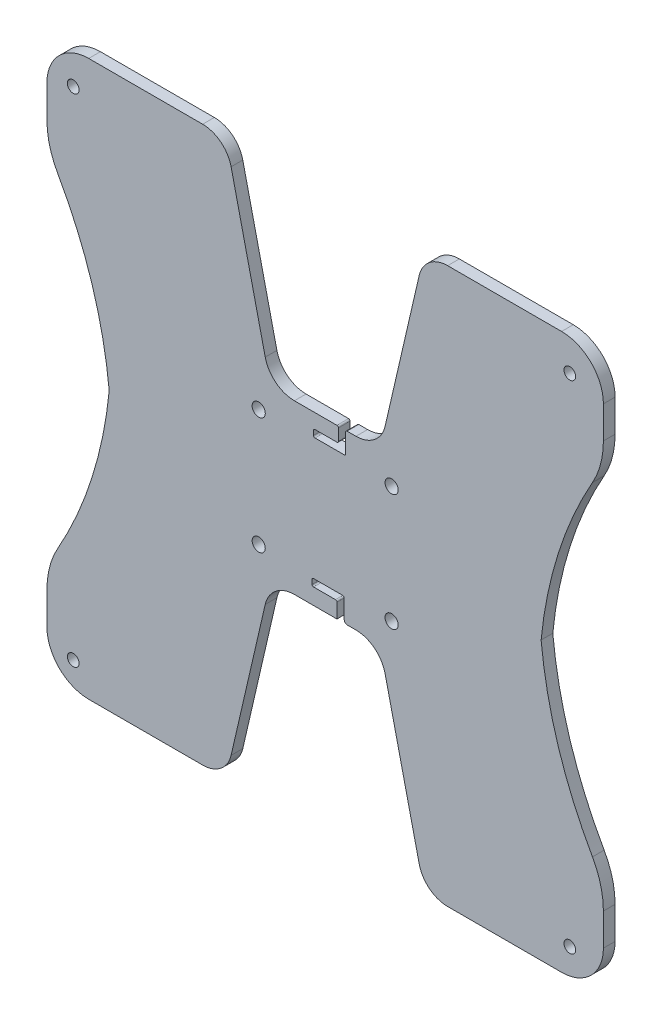
SolidWorks part; units mm, degrees
ref_plane "Front Plane" through (0, 0, 0) normal (0, 0, 1) x (1, 0, 0)
ref_plane "Top Plane" through (0, 0, 0) normal (0, 1, 0) x (1, 0, 0)
ref_plane "Right Plane" through (0, 0, 0) normal (1, 0, 0) x (0, 0, -1)
sketch "Sketch2" plane through (0, 0, 0) normal (0, 0, 1) x (1, 0, 0)
  line L3 (94.3754, -52.7044) -> (94.3754, -56.7044)
  line L4 (93.8754, -57.2044) -> (86.3754, -57.2044)
  line L5 (85.8754, -57.7044) -> (85.8754, -59.2044)
  line L6 (86.3754, -59.7044) -> (96.3754, -59.7044)
  line L7 (96.8754, -59.2044) -> (96.8754, -52.7044)
  line L8 (97.3754, -52.2044) -> (100.3754, -52.2044)
  line L9 (110.3627, -44.2602) -> (122.0425, 6.3307)
  line L10 (131.7862, 14.0812) -> (170.7845, 14.0812)
  line L11 (185.0955, -0.2297) -> (185.0955, -11.2297)
  line L16 (96.3754, -108.6331) -> (96.3754, -102.1331)
  line L17 (95.8754, -101.6331) -> (85.8754, -101.6331)
  line L18 (85.3754, -102.1331) -> (85.3754, -103.6331)
  line L19 (85.8754, -104.1331) -> (93.3754, -104.1331)
  line L20 (93.8754, -104.6331) -> (93.8754, -108.6331)
  line L26 (163.7717, -80.9188) -> (-81.9172, -80.9188) construction
  line L27 (97.3754, -109.6331) -> (100.3754, -109.6331)
  line L28 (185.0955, -161.6078) -> (185.0955, -150.6078)
  line L29 (131.7862, -175.9188) -> (170.7845, -175.9188)
  line L30 (110.3627, -117.5774) -> (122.0425, -168.1683)
  line L31 (185.0955, -161.6078) -> (-5.4045, -161.6078) construction
  line L32 (89.8455, -161.6078) -> (89.8455, -80.9188) construction
  line L33 (82.3155, -52.2044) -> (79.3155, -52.2044)
  line L34 (82.3155, -109.6331) -> (79.3155, -109.6331)
  line L35 (15.9192, -80.9188) -> (261.6081, -80.9188) construction
  line L36 (69.3282, -117.5774) -> (57.6484, -168.1683)
  line L37 (47.9047, -175.9188) -> (8.9064, -175.9188)
  line L38 (-5.4045, -161.6078) -> (-5.4045, -150.6078)
  line L39 (-5.4045, -0.2297) -> (-5.4045, -11.2297)
  line L40 (47.9047, 14.0812) -> (8.9064, 14.0812)
  line L41 (69.3282, -44.2602) -> (57.6484, 6.3307)
  line L42 (82.3155, -52.2044) -> (93.8754, -52.2044)
  line L43 (82.3155, -109.6331) -> (93.8754, -109.6331)
  line L44 (93.8754, -108.6331) -> (93.8754, -109.6331)
  line L45 (142.4554, -175.9188) -> (142.4554, 14.0812) construction
  arc A2 (94.3754, -52.7044) -> (93.8754, -52.2044) centre (93.8754, -52.7044) ccw
  arc A3 (93.8754, -57.2044) -> (94.3754, -56.7044) centre (93.8754, -56.7044) ccw
  arc A5 (85.8754, -59.2044) -> (86.3754, -59.7044) centre (86.3754, -59.2044) ccw
  arc A6 (86.3754, -57.2044) -> (85.8754, -57.7044) centre (86.3754, -57.7044) ccw
  arc A7 (96.3754, -59.7044) -> (96.8754, -59.2044) centre (96.3754, -59.2044) ccw
  arc A8 (97.3754, -52.2044) -> (96.8754, -52.7044) centre (97.3754, -52.7044) ccw
  arc A9 (100.3754, -52.2044) -> (110.3627, -44.2602) centre (100.3754, -41.9544) ccw
  arc A10 (131.7862, 14.0812) -> (122.0425, 6.3307) centre (131.7862, 4.0812) ccw
  arc A11 (185.0955, -0.2297) -> (170.7845, 14.0812) centre (170.7845, -0.2297) ccw
  arc A12 (181.353, -25.4269) -> (185.0955, -11.2297) centre (156.2955, -11.2297) ccw
  arc A13 (181.353, -25.4269) -> (163.7717, -80.9188) centre (303.5955, -94.6875) ccw
  arc A18 (96.3754, -108.6331) -> (97.3754, -109.6331) centre (97.3754, -108.6331) ccw
  arc A19 (96.3754, -102.1331) -> (95.8754, -101.6331) centre (95.8754, -102.1331) ccw
  arc A20 (85.8754, -101.6331) -> (85.3754, -102.1331) centre (85.8754, -102.1331) ccw
  arc A21 (85.3754, -103.6331) -> (85.8754, -104.1331) centre (85.8754, -103.6331) ccw
  arc A22 (93.8754, -104.6331) -> (93.3754, -104.1331) centre (93.3754, -104.6331) ccw
  arc A31 (79.3155, -109.6331) -> (69.3282, -117.5774) centre (79.3155, -119.8831) ccw
  arc A32 (181.353, -136.4106) -> (163.7717, -80.9188) centre (303.5955, -67.15) cw
  arc A33 (181.353, -136.4106) -> (185.0955, -150.6078) centre (156.2955, -150.6078) cw
  arc A34 (185.0955, -161.6078) -> (170.7845, -175.9188) centre (170.7845, -161.6078) cw
  arc A35 (131.7862, -175.9188) -> (122.0425, -168.1683) centre (131.7862, -165.9188) cw
  arc A36 (100.3754, -109.6331) -> (110.3627, -117.5774) centre (100.3754, -119.8831) cw
  arc A37 (47.9047, -175.9188) -> (57.6484, -168.1683) centre (47.9047, -165.9188) ccw
  arc A38 (-5.4045, -161.6078) -> (8.9064, -175.9188) centre (8.9064, -161.6078) ccw
  arc A39 (-1.6621, -136.4106) -> (-5.4045, -150.6078) centre (23.3955, -150.6078) ccw
  arc A40 (-1.6621, -136.4106) -> (15.9192, -80.9188) centre (-123.9045, -67.15) ccw
  arc A41 (-1.6621, -25.4269) -> (15.9192, -80.9188) centre (-123.9045, -94.6875) cw
  arc A42 (-1.6621, -25.4269) -> (-5.4045, -11.2297) centre (23.3955, -11.2297) cw
  arc A43 (-5.4045, -0.2297) -> (8.9064, 14.0812) centre (8.9064, -0.2297) cw
  arc A44 (47.9047, 14.0812) -> (57.6484, 6.3307) centre (47.9047, 4.0812) cw
  arc A45 (79.3155, -52.2044) -> (69.3282, -44.2602) centre (79.3155, -41.9544) cw
  dimension "D6" = 190.5
  dimension "D8" = 1
  dimension "D9" = 1
  dimension "D12" = 1
  dimension "D13" = 1
  dimension "D17" = 1
  dimension "D18" = 1
  dimension "D40" = 2
  dimension "D42" = 1
  dimension "D44" = 1
  dimension "D45" = 1
  dimension "D48" = 1
  dimension "D5" = 190
  dimension "D10" = 7.5
  dimension "D11" = 4
  dimension "D14" = 1.5
  dimension "D15" = 2.5
  dimension "D16" = 10
  dimension "D19" = 6.5
  dimension "D20" = 3
  dimension "D25" = 103
  dimension "D30" = 118.5
  dimension "D41" = 6.5
  dimension "D43" = 10
  dimension "D46" = 1.5
  dimension "D47" = 7.5
  dimension "D49" = 4
extrude "Boss-Extrude1" add sketch "Sketch2" along normal blind 4
sketch "Sketch3" plane through (0, 0, 4) normal (0, 0, 1) x (1, 0, 0)
  line L0 (170.7845, 14.0812) -> (131.7862, 14.0812) construction
  line L1 (-5.4045, -0.2297) -> (-5.4045, -11.2297) construction
  line L2 (8.9064, 14.0812) -> (170.7845, 14.0812) construction
  line L3 (89.8455, 14.0812) -> (89.8455, -175.9188) construction
  line L4 (67.0955, -60.9188) -> (112.5955, -60.9188) construction
  line L5 (8.9064, -175.9188) -> (170.7845, -175.9188) construction
  line L6 (89.8455, -80.9188) -> (119.7664, -80.9188) construction
  circle A0 centre (3.5955, 3.0812) radius 2
  circle A1 centre (3.5955, -166.9188) radius 2
  circle A2 centre (67.0955, -60.9188) radius 2.25
  circle A3 centre (112.5955, -60.9188) radius 2.25
  circle A4 centre (67.0955, -100.9188) radius 2.25
  circle A5 centre (112.5955, -100.9188) radius 2.25
  circle A6 centre (173.5955, -166.9188) radius 2
  circle A7 centre (173.5955, 3.0812) radius 2
  arc A8 (170.7845, -175.9188) -> (185.0955, -161.6078) centre (170.7845, -161.6078) ccw construction
  point P20 (89.8455, -60.9188)
  dimension "D1" = 170
  dimension "D2" = 20
  dimension "D3" = 170
  dimension "D4" = 11
  dimension "D5" = 45.5
  dimension "D6" = 40
  dimension "D7" = 9
  dimension "D8" = 4.5
  dimension "D9" = 4.5
  dimension "D10" = 4.5
  dimension "D11" = 4.5
extrude "Cut-Extrude1" cut sketch "Sketch3" against normal blind 4
ref_plane "Plane1" through (8.9064, 14.0812, 4) normal (-1, 0, 0) x (0, 0, 1)
sketch "Sketch5" plane through (0, 0, 4) normal (0, 0, 1) x (1, 0, 0)
  line L0 (47.9047, 14.0812) -> (8.9064, 14.0812) construction
  line L3 (44.9827, 14.0812) -> (44.9827, -175.9188) construction
  line L4 (8.9064, -175.9188) -> (47.9047, -175.9188) construction
  line L5 (-5.4045, -11.2297) -> (185.0955, -11.2297) construction
